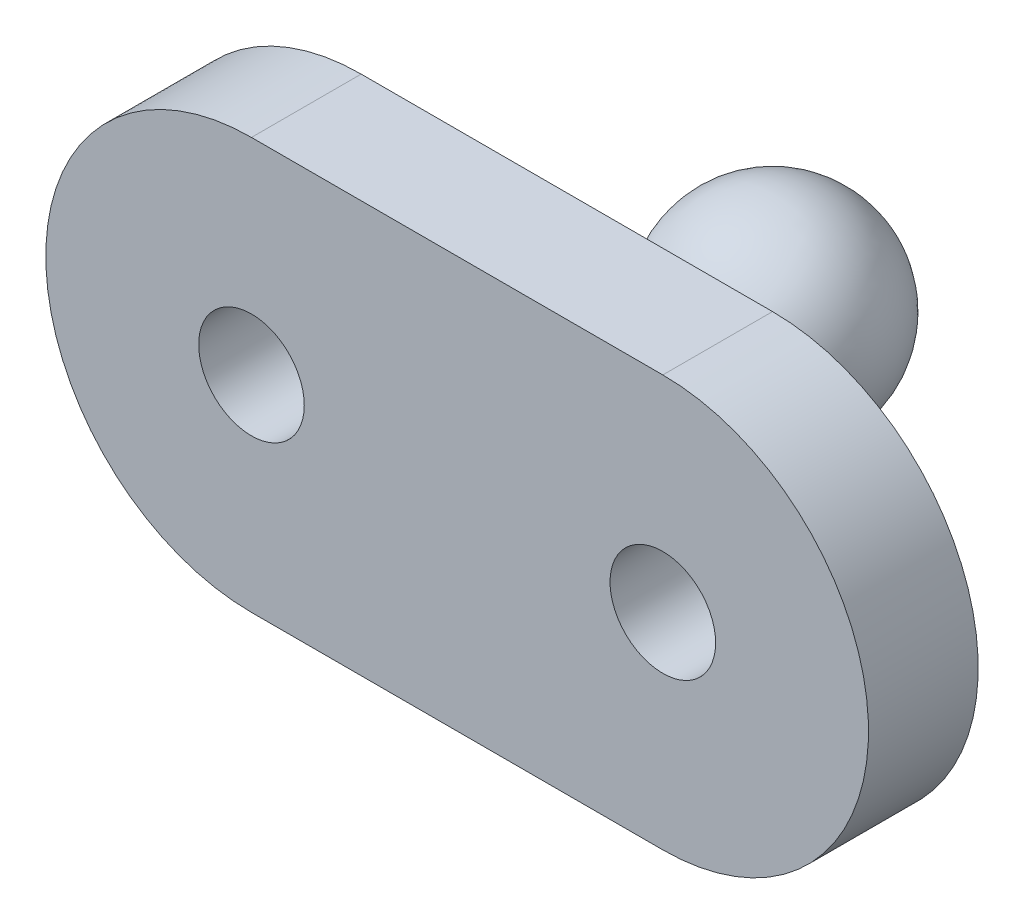
SolidWorks part; units mm, degrees
ref_plane "Front Plane" through (0, 0, 0) normal (0, 0, 1) x (1, 0, 0)
ref_plane "Top Plane" through (0, 0, 0) normal (0, 1, 0) x (1, 0, 0)
ref_plane "Right Plane" through (0, 0, 0) normal (1, 0, 0) x (0, 0, -1)
sketch "Sketch1" plane through (0, 0, 0) normal (0, 0, 1) x (1, 0, 0)
  line L0 (-7.5, 0) -> (7.5, 0) construction
  line L1 (-7.5, 7.5) -> (7.5, 7.5)
  line L2 (-7.5, -7.5) -> (7.5, -7.5)
  arc A0 (-7.5, 7.5) -> (-7.5, -7.5) centre (-7.5, 0) ccw
  arc A1 (7.5, -7.5) -> (7.5, 7.5) centre (7.5, 0) ccw
  circle A2 centre (7.5, 0) radius 1.925
  circle A3 centre (-7.5, 0) radius 1.925
  point P2 (0, 0)
  dimension "D1" = 7.5
  dimension "D3" = 3.85
  dimension "D4" = 3.85
  dimension "D2" = 15
extrude "Boss-Extrude1" add sketch "Sketch1" along normal blind 4
sketch "Sketch3" plane through (0, 0, 0) normal (0, 1, 0) x (1, 0, 0)
  line L0 (0, 7.5) -> (1.75, 7.5)
  line L1 (1.75, 7.5) -> (2.5, 0)
  line L2 (7.5, 0) -> (-7.5, 0) construction
  line L3 (2.5, 0) -> (0, 0)
  line L4 (0, 0) -> (0, 7.5)
  line L5 (0, 7.5) -> (0, 11.25)
  arc A0 (0, 3.75) -> (0, 11.25) centre (0, 7.5) ccw
  dimension "D1" = 7.5
  dimension "D2" = 2.5
  dimension "D3" = 1.75
  dimension "D4" = 7.5
revolve "Revolve1" add sketch "Sketch3" angle 360 about L4
fillet "Fillet1" radius 3 1 edges at (2.5, 0, 0)
